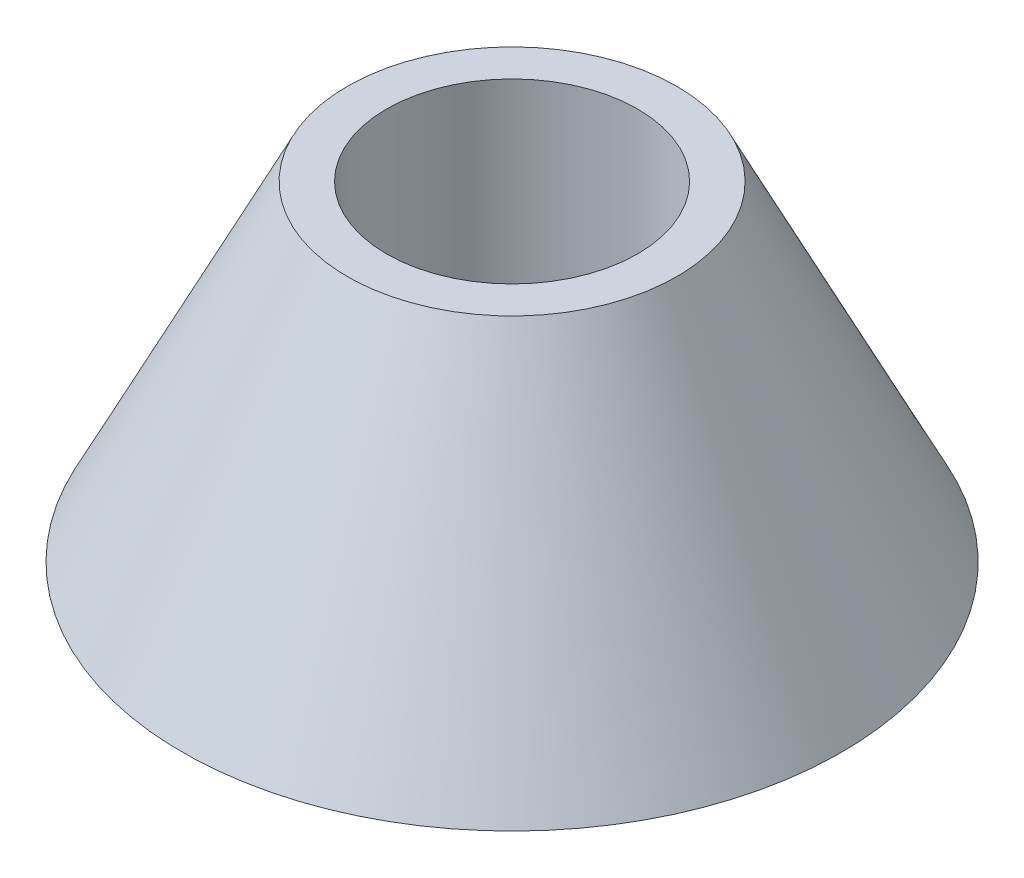
SolidWorks part; units mm, degrees
ref_plane "Plano frontal" through (0, 0, 0) normal (0, 0, 1) x (1, 0, 0)
ref_plane "Plano superior" through (0, 0, 0) normal (0, 1, 0) x (1, 0, 0)
ref_plane "Plano direito" through (0, 0, 0) normal (1, 0, 0) x (0, 0, -1)
sketch "Esboço1" plane through (0, 0, 0) normal (0, 0, 1) x (1, 0, 0)
  line L0 (0, 0) -> (0, 259.2324) construction
  line L1 (19.05, 50) -> (25, 50)
  line L2 (25, 50) -> (50, 0)
  line L3 (50, 0) -> (0, 0)
  line L4 (0, 0) -> (0, 10)
  line L5 (0, 10) -> (19.05, 10)
  line L6 (19.05, 10) -> (19.05, 50)
  dimension "D1" = 38.1
  dimension "D2" = 40
  dimension "D3" = 50
  dimension "D4" = 100
  dimension "D5" = 50
revolve "Revolução1" add sketch "Esboço1" angle 360 about L0
